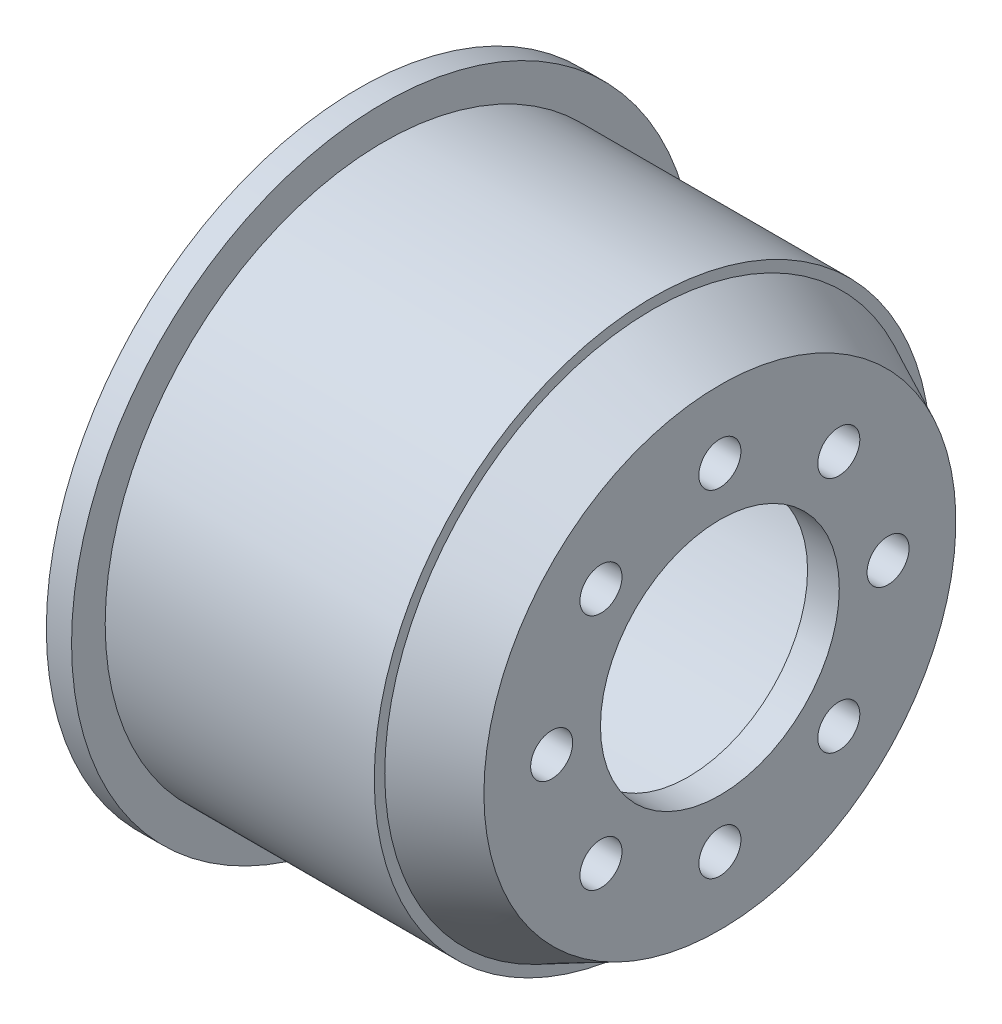
SolidWorks part; units mm, degrees
ref_plane "Front Plane" through (0, 0, 0) normal (0, 0, 1) x (1, 0, 0)
ref_plane "Top Plane" through (0, 0, 0) normal (0, 1, 0) x (1, 0, 0)
ref_plane "Right Plane" through (0, 0, 0) normal (1, 0, 0) x (0, 0, -1)
sketch "Sketch1" plane through (0, 0, 0) normal (0, 1, 0) x (1, 0, 0)
  line L0 (-37.2789, 0) -> (44.8184, 0) construction
  line L7 (8.9363, 8.625) -> (8.9363, 14.0316)
  line L11 (-12.5637, 14.55) -> (3.1724, 14.55)
  line L12 (-12.5637, 14.55) -> (-12.5637, 16.55)
  line L13 (-11.0637, 16.55) -> (4.9363, 16.55)
  line L21 (7.0506, 12.712) -> (7.0506, 7.1)
  line L23 (4.9363, 15.9273) -> (8.9363, 14.0316)
  line L26 (7.0506, 7.1) -> (8.9363, 7.1)
  line L27 (8.9363, 7.1) -> (8.9363, 8.625)
  line L28 (3.1724, 14.55) -> (7.0506, 12.712)
  line L30 (4.9363, 15.9273) -> (4.9363, 16.55)
  line L31 (-12.5637, 16.55) -> (-12.5637, 18.55)
  line L32 (-12.5637, 18.55) -> (-11.0637, 18.55)
  line L33 (-11.0637, 18.55) -> (-11.0637, 16.55)
  point P4 (7.9363, 16.8502)
  point P5 (4.4149, 14.4498)
  point P16 (8.4149, 12.5541)
  dimension "D1" = 29.1
  dimension "D2" = 4
  dimension "D4" = 2
  dimension "D5" = 1.5
  dimension "D6" = 16
  dimension "D7" = 21.5
  dimension "D8" = 14.2
  dimension "D9" = 28.0632
  dimension "D10" = 2
  dimension "D12" = 33.1
  dimension "D3" = 2
revolve "Revolve1" add sketch "Sketch1" angle 360 about L0
sketch "Sketch2" plane through (8.9363, 0, 0) normal (1, 0, 0) x (0, 0, -1)
  line L0 (0, 14.0316) -> (0, -14.0316) construction
  line L1 (-14.0316, 0) -> (14.0316, 0) construction
  line L2 (-13.3673, 5.6184) -> (13.3673, -5.6184) construction
  circle A0 centre (0, 0) radius 14.0316 construction
  circle A1 centre (0, 0) radius 10 construction
  circle A2 centre (0, 10) radius 1.25
  circle A3 centre (7.0711, 7.0711) radius 1.25
  circle A4 centre (10, 0) radius 1.25
  circle A5 centre (7.0711, -7.0711) radius 1.25
  circle A6 centre (0, -10) radius 1.25
  circle A7 centre (-7.0711, -7.0711) radius 1.25
  circle A8 centre (-10, 0) radius 1.25
  circle A9 centre (-7.0711, 7.0711) radius 1.25
  arc A21 (13.3673, -5.6184) -> (14.0093, -3.7403) centre (0, 0) ccw construction
  point P28 (0, 0)
  point P46 (0, 0)
  point P95 (0, 0)
  dimension "D1" = 20
  dimension "D2" = 2.5
  dimension "D3" = 8
extrude "Cut-Extrude1" cut sketch "Sketch2" against normal blind 5
sketch3d "3DSketch1"
  point P0 (6.2337, 4.4246, 14.6592)
ref_plane "Plane1" through (-2.9537, -0.0859, 12.4482) normal (-0.2309, -0.0067, 0.973) x (0.972, -0.0459, 0.2303)
sketch "Sketch3" plane through (-2.9537, -0.0859, 12.4482) normal (-0.2309, -0.0067, 0.973) x (0.972, -0.0459, 0.2303)
  ellipse E0 centre (9.9983, 5.3304) end of major axis (9.9983, 2.8304) minor radius 1.5
  ellipse E1 centre (4.7983, 0.2126) end of major axis (4.0932, 16.1243) minor radius 3.677 construction
  dimension "D1" = 5.2
  dimension "D2" = 3
  dimension "D3" = 5
